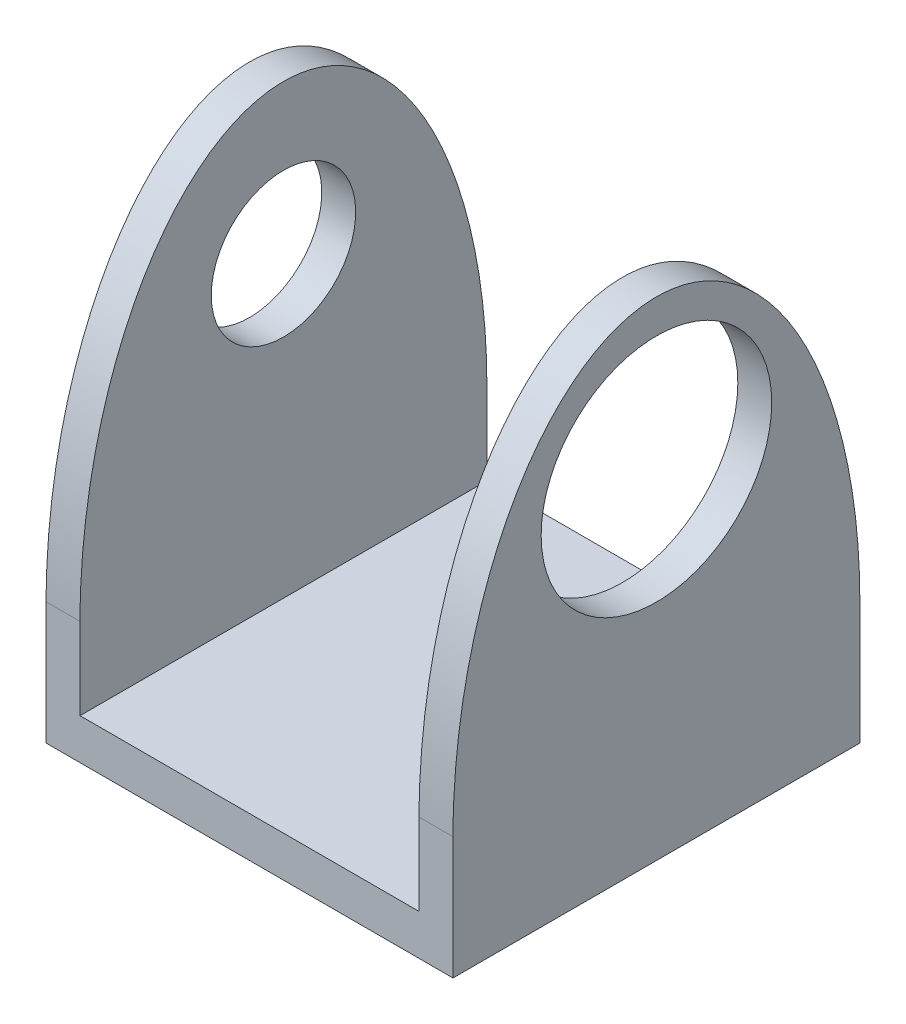
SolidWorks part; units mm, degrees
ref_plane "Front Plane" through (0, 0, 0) normal (0, 0, 1) x (1, 0, 0)
ref_plane "Top Plane" through (0, 0, 0) normal (0, 1, 0) x (1, 0, 0)
ref_plane "Right Plane" through (0, 0, 0) normal (1, 0, 0) x (0, 0, -1)
sketch "Sketch1" plane through (0, 0, 0) normal (0, 0, 1) x (1, 0, 0)
  line L0 (-3.3539, 6.8522) -> (-3.3539, -2.2918)
  line L1 (-3.3539, -2.2918) -> (4.2661, -2.2918)
  line L2 (4.2661, -2.2918) -> (4.2661, 6.8522)
  line L3 (3.6311, 6.8522) -> (3.6311, -1.5298)
  line L4 (3.6311, -1.5298) -> (-2.7189, -1.5298)
  line L5 (-2.7189, -1.5298) -> (-2.7189, 6.8522)
  line L6 (-2.7189, 6.8522) -> (-3.3539, 6.8522)
  line L7 (3.6311, 6.8522) -> (4.2661, 6.8522)
  dimension "D1" = 6.35
  dimension "D2" = 7.62
  dimension "D3" = 0.635
  dimension "D4" = 8.382
  dimension "D5" = 9.144
  dimension "D6" = 8.382
extrude "Boss-Extrude1" add sketch "Sketch1" along normal blind 7.62
sketch "Sketch2" plane through (-3.3539, 0, 0) normal (-1, 0, 0) x (0, 0, 1)
  line L0 (7.62, 6.8522) -> (0, 6.8522) construction
  line L1 (3.81, -2.2918) -> (3.81, 6.8522) construction
  point P0 (3.81, 4.0582)
  dimension "D1" = 2.794
hole_wizard "#6-32 Tapped Hole1" positions "Sketch3" profile "Sketch4" tap size "#6-32" standard "ANSI Inch" end condition up to next
sketch "Sketch3" plane through (-3.3539, 0, 0) normal (-1, 0, 0) x (0, 0, 1)
  point P0 (3.81, 4.0582)
sketch "Sketch4" plane through (-3.3539, 4.0582, 3.81) normal (0, 1, 0) x (0, 0, 1)
  line L0 (0, 0) -> (0, 0.635)
  line L1 (0, 0.635) -> (1.3525, 0.635)
  line L2 (1.3525, 0.635) -> (1.3525, 0)
  line L5 (1.3525, 0) -> (0, 0)
  line L11 (0, -6.35) -> (0, 107.95) construction
  dimension "Thread Major Dia." = 2.7051
  dimension "Thru Tap Drill Depth" = 0.635
sketch "Sketch5" plane through (4.2661, 0, 0) normal (1, 0, 0) x (0, 0, -1)
  point P0 (-3.81, 4.0582)
sketch "Sketch6" plane through (4.2661, 0, 0) normal (1, 0, 0) x (0, 0, -1)
  circle A0 centre (-3.81, 4.0582) radius 2.159
extrude "Cut-Extrude1" cut sketch "Sketch6" against normal up to next
sketch "Sketch12" plane through (-3.3539, 0, 0) normal (-1, 0, 0) x (0, 0, 1)
  line L0 (3.81, -2.2918) -> (3.81, 6.8522) construction
  line L1 (7.62, -2.2918) -> (0, -2.2918) construction
  line L2 (7.62, 6.8522) -> (0, 6.8522) construction
sketch "Sketch26" plane through (4.2661, 0, 0) normal (1, 0, 0) x (0, 0, -1)
  line L1 (-3.81, -2.2918) -> (-3.81, 6.8522) construction
  line L2 (-7.62, -2.2918) -> (-7.62, 6.8522) construction
  line L3 (0, 0) -> (0, 6.8522)
  line L4 (0, 6.8522) -> (-7.62, 6.8522)
  line L5 (-7.62, 6.8522) -> (-7.62, 0)
  ellipse E0 centre (-3.81, 0) end of major axis (-3.81, 6.8522) minor radius 3.81 (0, 0) -> (-7.62, 0) ccw
  line M2 (0, -2.2918) -> (0, 6.8522)
  line M3 (0, 6.8522) -> (-7.62, 6.8522)
  line M4 (-7.62, 6.8522) -> (-7.62, -2.2918)
extrude "Cut-Extrude6" cut sketch "Sketch26" against normal through all contours E0 M2 M3 | E0 L4 M4
sketch "Sketch27" plane through (0, -2.2918, 0) normal (0, -1, 0) x (1, 0, 0)
  line L0 (3.2591, 6.2374) -> (-2.0856, 6.2374)
  line L1 (-2.0856, 6.2374) -> (-2.0856, 1.4479)
  line L2 (-2.0856, 1.4479) -> (3.2591, 1.4479)
  line L3 (3.2591, 1.4479) -> (3.2591, 6.2374)
extrude "Boss-Extrude2" add sketch "Sketch27" along normal blind 0.0254
